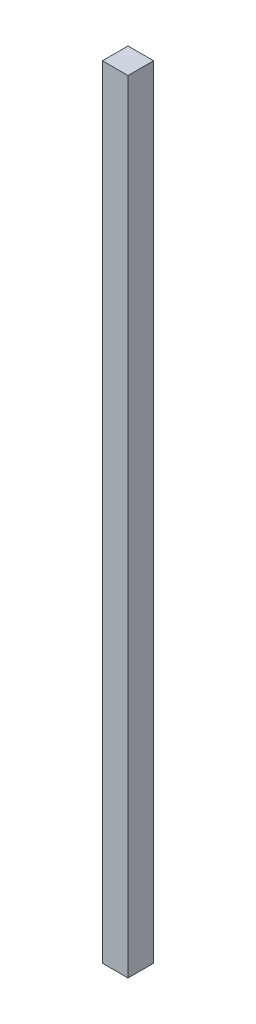
SolidWorks part; units mm, degrees
ref_plane "Front Plane" through (0, 0, 0) normal (0, 0, 1) x (1, 0, 0)
ref_plane "Top Plane" through (0, 0, 0) normal (0, 1, 0) x (1, 0, 0)
ref_plane "Right Plane" through (0, 0, 0) normal (1, 0, 0) x (0, 0, -1)
sketch "Sketch1" plane through (0, 0, 0) normal (0, 1, 0) x (1, 0, 0)
  line L1 (-12.7, -12.7) -> (12.7, -12.7)
  line L2 (-12.7, -12.7) -> (-12.7, 12.7)
  line L3 (-12.7, 12.7) -> (12.7, 12.7)
  line L4 (12.7, -12.7) -> (12.7, 12.7)
  line L5 (-12.7, -12.7) -> (12.7, 12.7) construction
  line L6 (-12.7, 12.7) -> (12.7, -12.7) construction
  point P0 (0, 0)
  dimension "D1" = 25.4
  dimension "D2" = 25.4
extrude "Boss-Extrude1" add sketch "Sketch1" along normal blind 775.97
